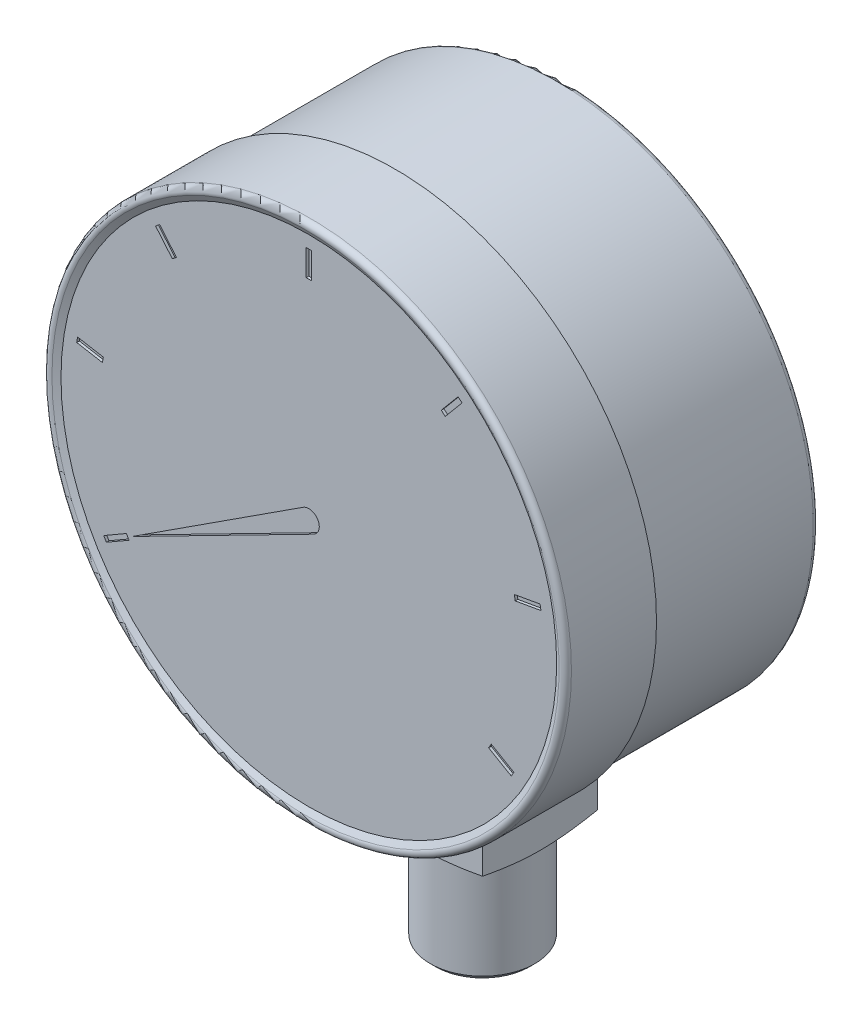
SolidWorks part; units mm, degrees
ref_plane "Horní" through (0, 0, 0) normal (0, 0, 1) x (1, 0, 0)
ref_plane "Přední" through (0, 0, 0) normal (0, 1, 0) x (1, 0, 0)
ref_plane "Pravá" through (0, 0, 0) normal (1, 0, 0) x (0, 0, -1)
sketch "Skica1" plane through (0, 0, 0) normal (1, 0, 0) x (0, 0, -1)
  line L0 (0, 50) -> (1.5, 47.4019)
  line L1 (0, 50) -> (18, 50)
  line L4 (50, 49) -> (50, 0)
  line L7 (50, 0) -> (1.5, 0)
  line L8 (0, 0) -> (-34.5616, 0) construction
  line L10 (1.5, 47.4019) -> (1.5, 0)
  line L12 (18, 50) -> (18, 49)
  line L13 (18, 49) -> (50, 49)
  dimension "D2" = 100
  dimension "D4" = 98
  dimension "D7" = 30
  dimension "D8" = 1.5
  dimension "D9" = 50
  dimension "D12" = 18
revolve "Rotovat1" add sketch "Skica1" angle 360 about L8
fillet "Zaoblit1" radius 1 2 edges at (-50, 0, 0) (-49, 0, -50)
sketch "Skica2" plane through (0, 0, -1.5) normal (0, 0, 1) x (1, 0, 0)
  line L0 (0, 45) -> (0, 0) construction
  line L3 (0.5, 40) -> (0.5, 45)
  line L4 (0.5, 40) -> (-0.5, 40)
  line L5 (0.5, 45) -> (-0.5, 45)
  line L6 (-0.5, 40) -> (-0.5, 45)
  dimension "D1" = 45
  dimension "D2" = 1
  dimension "D3" = 5
extrude "Odebrat vysunutím1" cut sketch "Skica2" against normal blind 0.5
pattern_circular "Kruhové pole1" count 9 over 360 about axis through (0, 0, 0) along (0, 0, 1) skipping 4, 5 of "Odebrat vysunutím1"
sketch "Skica3" plane through (0, 0, -1.5) normal (0, 0, 1) x (1, 0, 0)
  line L0 (-1.0875, 1.6785) -> (-33.775, -19.5)
  line L1 (-33.775, -19.5) -> (0.9099, -1.7811)
  line L2 (0, 0) -> (-33.775, -19.5) construction
  line L3 (-38.7211, -22.933) -> (-34.391, -20.433) construction
  arc A0 (0.9099, -1.7811) -> (-1.0875, 1.6785) centre (0, 0) ccw
  dimension "D1" = 2
  dimension "D2" = 39
extrude "Odebrat vysunutím2" cut sketch "Skica3" against normal blind 0.5
sketch "Skica4" plane through (0, 0, 0) normal (0, 1, 0) x (1, 0, 0)
  line L0 (-49, 0.7321) -> (49, 0.7321) construction
  line L1 (-11, 45.7321) -> (11, 45.7321)
  line L2 (-11, 45.7321) -> (-11, 23.7321)
  line L3 (-11, 23.7321) -> (11, 23.7321)
  line L4 (11, 45.7321) -> (11, 23.7321)
  line L5 (0, 45.7321) -> (0, 23.7321) construction
  dimension "D1" = 23
  dimension "D2" = 22
extrude "Přidat vysunutím1" add sketch "Skica4" against normal blind 89
sketch "Skica5" plane through (0, 0, 0) normal (1, 0, 0) x (0, 0, -1)
  line L0 (34.7321, -89) -> (34.7321, -47.7493) construction
  line L1 (23.7321, -89) -> (45.7321, -89) construction
  line L2 (45.7321, -47.7493) -> (23.7321, -47.7493) construction
  line L3 (3.7321, -60.3731) -> (24.7321, -66)
  line L5 (24.7321, -66) -> (24.7321, -86)
  line L6 (24.7321, -86) -> (32.2321, -86)
  line L7 (32.2321, -86) -> (32.2321, -89)
  line L8 (3.7321, -89) -> (32.2321, -89)
  line L9 (3.7321, -89) -> (3.7321, -60.3731)
  line L10 (23.7321, -89) -> (23.7321, -47.7493) construction
  line L11 (23.7321, -89) -> (23.7321, -47.7493) construction
  dimension "D1" = 23
  dimension "D2" = 5
  dimension "D3" = 3
  dimension "D4" = 20
  dimension "D5" = 20
  dimension "D6" = 15
revolve "Odebrat rotací1" cut sketch "Skica5" angle 360 about L0
chamfer "Zkosení1" distance 1 angle 45 1 edges at (0, -86, -44.7321)
